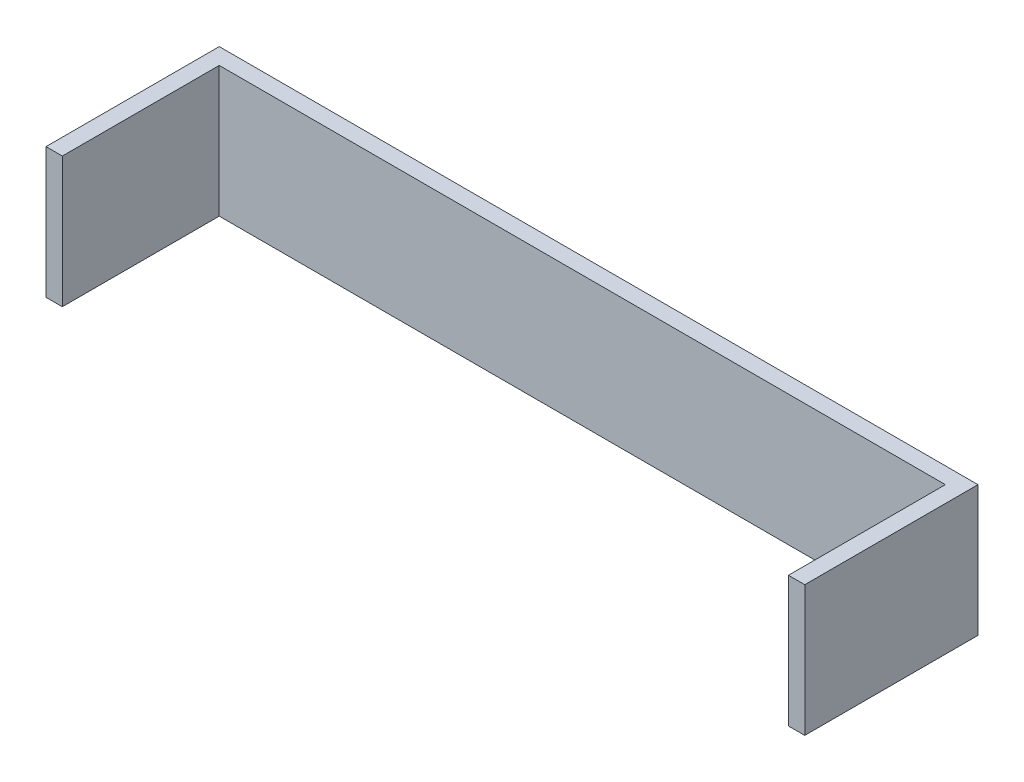
SolidWorks part; units mm, degrees
ref_plane "Front Plane" through (0, 0, 0) normal (0, 0, 1) x (1, 0, 0)
ref_plane "Top Plane" through (0, 0, 0) normal (0, 1, 0) x (1, 0, 0)
ref_plane "Right Plane" through (0, 0, 0) normal (1, 0, 0) x (0, 0, -1)
sketch "Sketch1" plane through (0, 0, 0) normal (0, 0, 1) x (1, 0, 0)
  line L1 (-73.8187, -12.7) -> (73.8188, -12.7)
  line L2 (-73.8187, -12.7) -> (-73.8187, 12.7)
  line L3 (-73.8187, 12.7) -> (73.8188, 12.7)
  line L4 (73.8188, -12.7) -> (73.8188, 12.7)
  line L5 (-73.8187, -12.7) -> (73.8188, 12.7) construction
  line L6 (-73.8187, 12.7) -> (73.8188, -12.7) construction
  point P0 (0, 0)
  dimension "D1" = 147.6375
  dimension "D2" = 25.4
extrude "Boss-Extrude1" add sketch "Sketch1" along normal blind 3.175
sketch "Sketch2" plane through (0, 0, 3.175) normal (0, 0, 1) x (1, 0, 0)
  line L0 (-73.8187, -12.7) -> (73.8188, -12.7) construction
  line L1 (-73.8187, 12.7) -> (-70.6437, 12.7)
  line L2 (-73.8187, 12.7) -> (-73.8187, -12.7)
  line L3 (-73.8187, -12.7) -> (-70.6437, -12.7)
  line L4 (-70.6437, 12.7) -> (-70.6437, -12.7)
  dimension "D1" = 3.175
extrude "Boss-Extrude2" add sketch "Sketch2" along normal blind 30.5359
mirror "Mirror1" about plane through (0, 0, 0) normal (1, 0, 0) of "Boss-Extrude2"
equation "\"support width\"= 5.5625 + 0.125 + 0.125in"
equation "\"support with interior\"= 5.5625in"
equation "\"support length\"= 1in"
equation "\"support extrude\"= 0.125in"
equation "\"D1@Sketch1\"=\"support width\""
equation "\"D2@Sketch1\"=\"support length\""
equation "\"D1@Boss-Extrude1\"=\"support extrude\""
equation "\"support sides length\"= 0.125in"
equation "\"D1@Sketch2\"=\"support sides length\""
equation "\"support sides extrude\"= 2.6544 / 2 - 0.125in"
equation "\"D1@Boss-Extrude2\"=\"support sides extrude\""
